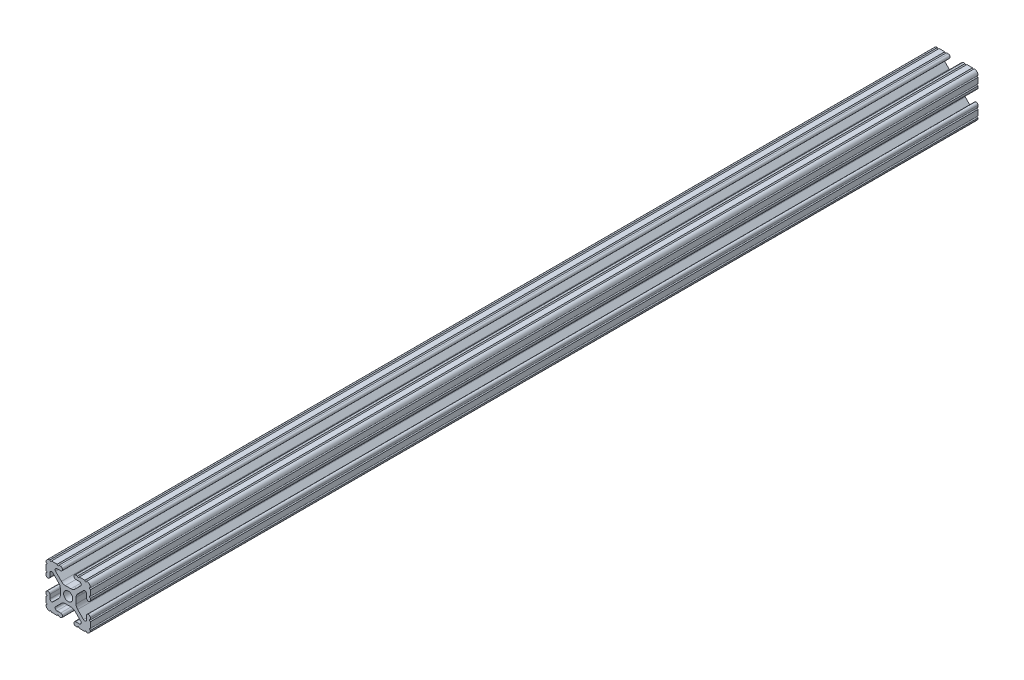
SolidWorks part; units mm, degrees
ref_plane "Front Plane" through (0, 0, 0) normal (0, 0, 1) x (1, 0, 0)
ref_plane "Top Plane" through (0, 0, 0) normal (0, 1, 0) x (1, 0, 0)
ref_plane "Right Plane" through (0, 0, 0) normal (1, 0, 0) x (0, 0, -1)
sketch "Sketch1" plane through (0, 0, 0) normal (0, 0, 1) x (1, 0, 0)
  line L0 (-12.7, -6.3331) -> (-12.7, -9.5504)
  line L1 (-9.5504, -12.7) -> (-6.3331, -12.7)
  line L2 (-5.3171, -12.7) -> (-4.3434, -12.7)
  line L3 (-4.3434, -10.4902) -> (-6.4748, -10.4902)
  line L4 (-7.1932, -8.7558) -> (-3.8632, -5.4257)
  line L5 (-1.6181, -4.4958) -> (1.6181, -4.4958)
  line L6 (3.8632, -5.4257) -> (7.1932, -8.7558)
  line L7 (6.4748, -10.4902) -> (4.3434, -10.4902)
  line L8 (4.3434, -12.7) -> (5.3171, -12.7)
  line L9 (6.3331, -12.7) -> (9.5504, -12.7)
  line L10 (12.7, -9.5504) -> (12.7, -6.3331)
  line L11 (12.7, -5.3171) -> (12.7, -4.3434)
  line L12 (10.4902, -4.3434) -> (10.4902, -6.4748)
  line L13 (8.7558, -7.1932) -> (5.4257, -3.8632)
  line L14 (4.4958, -1.6181) -> (4.4958, 1.6181)
  line L15 (5.4257, 3.8632) -> (8.7558, 7.1932)
  line L16 (10.4902, 6.4748) -> (10.4902, 4.3434)
  line L17 (12.7, 4.3434) -> (12.7, 5.3171)
  line L18 (12.7, 6.3331) -> (12.7, 9.5504)
  line L19 (9.5504, 12.7) -> (6.3331, 12.7)
  line L20 (5.3171, 12.7) -> (4.3434, 12.7)
  line L21 (4.3434, 10.4902) -> (6.4748, 10.4902)
  line L22 (7.1932, 8.7558) -> (3.8632, 5.4257)
  line L23 (1.6181, 4.4958) -> (-1.6181, 4.4958)
  line L24 (-3.8632, 5.4257) -> (-7.1932, 8.7558)
  line L25 (-6.4748, 10.4902) -> (-4.3434, 10.4902)
  line L26 (-4.3434, 12.7) -> (-5.3171, 12.7)
  line L27 (-6.3331, 12.7) -> (-9.5504, 12.7)
  line L28 (-12.7, 9.5504) -> (-12.7, 6.3331)
  line L29 (-12.7, 5.3171) -> (-12.7, 4.3434)
  line L30 (-10.4902, 4.3434) -> (-10.4902, 6.4748)
  line L31 (-8.7558, 7.1932) -> (-5.4257, 3.8632)
  line L32 (-4.4958, 1.6181) -> (-4.4958, -1.6181)
  line L33 (-5.4257, -3.8632) -> (-8.7558, -7.1932)
  line L34 (-10.4902, -6.4748) -> (-10.4902, -4.3434)
  line L35 (-12.7, -4.3434) -> (-12.7, -5.3171)
  circle A0 centre (0, 0) radius 2.6035
  arc A1 (-12.7, -5.3171) -> (-12.7, -6.3331) centre (-12.7, -5.8251) cw
  arc A2 (-12.7, -9.5504) -> (-12.6998, -10.5664) centre (-12.7, -10.0584) cw
  arc A3 (-12.6998, -10.5664) -> (-10.5664, -12.6998) centre (-10.5918, -10.5918) ccw
  arc A4 (-10.5664, -12.6998) -> (-9.5504, -12.7) centre (-10.0584, -12.7) cw
  arc A5 (-6.3331, -12.7) -> (-5.3171, -12.7) centre (-5.8251, -12.7) cw
  arc A6 (-4.3434, -12.7) -> (-4.3434, -10.4902) centre (-4.3434, -11.5951) ccw
  arc A7 (-6.4748, -10.4902) -> (-7.1932, -8.7558) centre (-6.4748, -9.4742) cw
  arc A8 (-3.8632, -5.4257) -> (-1.6181, -4.4958) centre (-1.6181, -7.6708) cw
  arc A9 (1.6181, -4.4958) -> (3.8632, -5.4257) centre (1.6181, -7.6708) cw
  arc A10 (7.1932, -8.7558) -> (6.4748, -10.4902) centre (6.4748, -9.4742) cw
  arc A11 (4.3434, -10.4902) -> (4.3434, -12.7) centre (4.3434, -11.5951) ccw
  arc A12 (5.3171, -12.7) -> (6.3331, -12.7) centre (5.8251, -12.7) cw
  arc A13 (9.5504, -12.7) -> (10.5664, -12.6998) centre (10.0584, -12.7) cw
  arc A14 (10.5664, -12.6998) -> (12.6998, -10.5664) centre (10.5918, -10.5918) ccw
  arc A15 (12.6998, -10.5664) -> (12.7, -9.5504) centre (12.7, -10.0584) cw
  arc A16 (12.7, -6.3331) -> (12.7, -5.3171) centre (12.7, -5.8251) cw
  arc A17 (12.7, -4.3434) -> (10.4902, -4.3434) centre (11.5951, -4.3434) ccw
  arc A18 (10.4902, -6.4748) -> (8.7558, -7.1932) centre (9.4742, -6.4748) cw
  arc A19 (5.4257, -3.8632) -> (4.4958, -1.6181) centre (7.6708, -1.6181) cw
  arc A20 (4.4958, 1.6181) -> (5.4257, 3.8632) centre (7.6708, 1.6181) cw
  arc A21 (8.7558, 7.1932) -> (10.4902, 6.4748) centre (9.4742, 6.4748) cw
  arc A22 (10.4902, 4.3434) -> (12.7, 4.3434) centre (11.5951, 4.3434) ccw
  arc A23 (12.7, 5.3171) -> (12.7, 6.3331) centre (12.7, 5.8251) cw
  arc A24 (12.7, 9.5504) -> (12.6998, 10.5664) centre (12.7, 10.0584) cw
  arc A25 (12.6998, 10.5664) -> (10.5664, 12.6998) centre (10.5918, 10.5918) ccw
  arc A26 (10.5664, 12.6998) -> (9.5504, 12.7) centre (10.0584, 12.7) cw
  arc A27 (6.3331, 12.7) -> (5.3171, 12.7) centre (5.8251, 12.7) cw
  arc A28 (4.3434, 12.7) -> (4.3434, 10.4902) centre (4.3434, 11.5951) ccw
  arc A29 (6.4748, 10.4902) -> (7.1932, 8.7558) centre (6.4748, 9.4742) cw
  arc A30 (3.8632, 5.4257) -> (1.6181, 4.4958) centre (1.6181, 7.6708) cw
  arc A31 (-1.6181, 4.4958) -> (-3.8632, 5.4257) centre (-1.6181, 7.6708) cw
  arc A32 (-7.1932, 8.7558) -> (-6.4748, 10.4902) centre (-6.4748, 9.4742) cw
  arc A33 (-4.3434, 10.4902) -> (-4.3434, 12.7) centre (-4.3434, 11.5951) ccw
  arc A34 (-5.3171, 12.7) -> (-6.3331, 12.7) centre (-5.8251, 12.7) cw
  arc A35 (-9.5504, 12.7) -> (-10.5664, 12.6998) centre (-10.0584, 12.7) cw
  arc A36 (-10.5664, 12.6998) -> (-12.6998, 10.5664) centre (-10.5918, 10.5918) ccw
  arc A37 (-12.6998, 10.5664) -> (-12.7, 9.5504) centre (-12.7, 10.0584) cw
  arc A38 (-12.7, 6.3331) -> (-12.7, 5.3171) centre (-12.7, 5.8251) cw
  arc A39 (-12.7, 4.3434) -> (-10.4902, 4.3434) centre (-11.5951, 4.3434) ccw
  arc A40 (-10.4902, 6.4748) -> (-8.7558, 7.1932) centre (-9.4742, 6.4748) cw
  arc A41 (-5.4257, 3.8632) -> (-4.4958, 1.6181) centre (-7.6708, 1.6181) cw
  arc A42 (-4.4958, -1.6181) -> (-5.4257, -3.8632) centre (-7.6708, -1.6181) cw
  arc A43 (-8.7558, -7.1932) -> (-10.4902, -6.4748) centre (-9.4742, -6.4748) cw
  arc A44 (-10.4902, -4.3434) -> (-12.7, -4.3434) centre (-11.5951, -4.3434) ccw
extrude "Boss-Extrude1" add sketch "Sketch1" against normal blind 508
